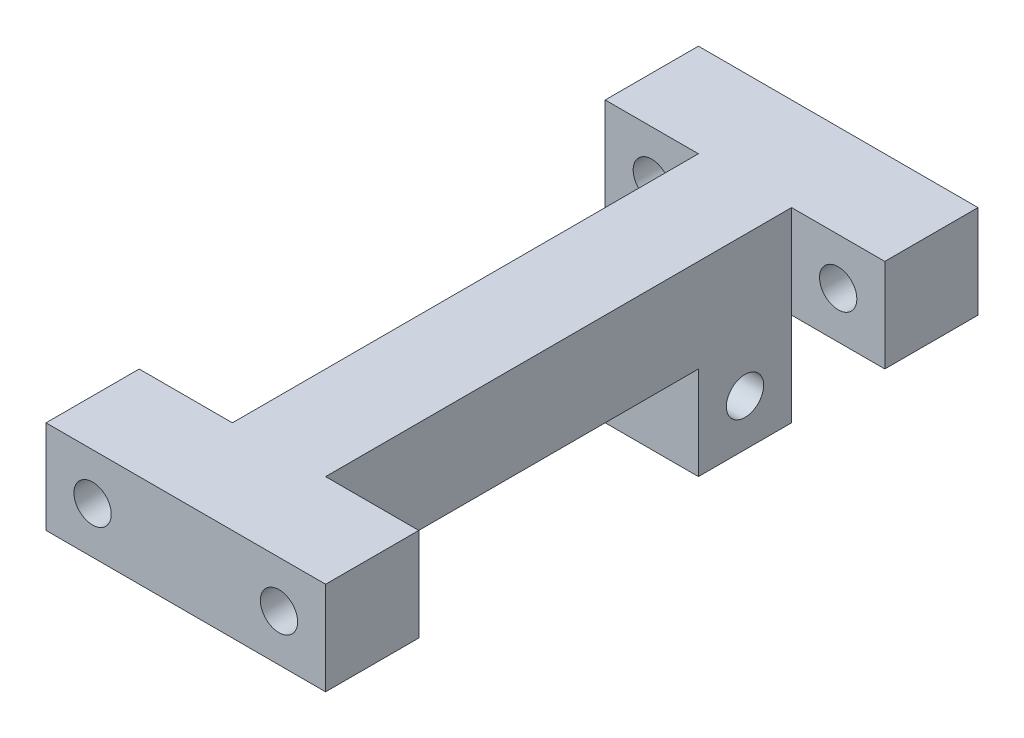
SolidWorks part; units mm, degrees
material "Cast Stainless Steel"
ref_plane "Front Plane" through (0, 0, 0) normal (0, 0, 1) x (1, 0, 0)
ref_plane "Top Plane" through (0, 0, 0) normal (0, 1, 0) x (1, 0, 0)
ref_plane "Right Plane" through (0, 0, 0) normal (1, 0, 0) x (0, 0, -1)
sketch "Sketch2" plane through (0, 0, 0) normal (1, 0, 0) x (0, 0, -1)
  line L1 (0, 0) -> (250, 0)
  line L2 (0, 0) -> (0, 100)
  line L3 (0, 100) -> (250, 100)
  line L4 (250, 0) -> (250, 100)
  dimension "D1" = 100
  dimension "D2" = 250
extrude "Boss-Extrude1" add sketch "Sketch2" along normal blind 50
sketch "Sketch3" plane through (50, 0, 0) normal (1, 0, 0) x (0, 0, -1)
  line L0 (0, 0) -> (50, 0)
  line L1 (0, 0) -> (250, 0) construction
  line L2 (250, 0) -> (200, 0)
  line L3 (50, 0) -> (50, 50)
  line L4 (50, 50) -> (200, 50)
  line L5 (200, 50) -> (200, 0)
  line L6 (50, 0) -> (200, 0)
  line M5 (0, 0) -> (250, 0)
  dimension "D1" = 50
  dimension "D2" = 50
  dimension "D3" = 50
extrude "Cut-Extrude1" cut sketch "Sketch3" against normal blind 109 contours L5 L4 L3 M5
sketch "Sketch4" plane through (50, 0, 0) normal (1, 0, 0) x (0, 0, -1)
  circle A0 centre (25, 25) radius 10
  circle A1 centre (225, 25) radius 10
  dimension "D1" = 20
  dimension "D2" = 20
extrude "Cut-Extrude2" cut sketch "Sketch4" against normal blind 109
sketch "Sketch5" plane through (50, 0, 0) normal (1, 0, 0) x (0, 0, -1)
  line L0 (250, 0) -> (250, 100) construction
  line L1 (0, 100) -> (250, 100)
  line L2 (0, 100) -> (0, 50)
  line L3 (0, 50) -> (250, 50)
  line L4 (250, 100) -> (250, 50)
extrude "Boss-Extrude2" add sketch "Sketch5" along normal blind 50
ref_plane "Plane1" through (25, 0, 0) normal (1, 0, 0) x (0, 0, -1)
mirror "Mirror1" about plane through (25, 0, 0) normal (1, 0, 0) of "Boss-Extrude2"
sketch "Sketch8" plane through (0, 0, 0) normal (0, 0, 1) x (1, 0, 0)
  line L1 (-50, 50) -> (100, 50)
  line L2 (-50, 50) -> (-50, 100)
  line L3 (-50, 100) -> (100, 100)
  line L4 (100, 50) -> (100, 100)
extrude "Boss-Extrude3" add sketch "Sketch8" along normal blind 50
sketch "Sketch9" plane through (0, 0, -250) normal (0, 0, -1) x (-1, 0, 0)
  line L1 (-100, 50) -> (50, 50)
  line L2 (-100, 50) -> (-100, 100)
  line L3 (-100, 100) -> (50, 100)
  line L4 (50, 50) -> (50, 100)
extrude "Boss-Extrude4" add sketch "Sketch9" along normal blind 50
sketch "Sketch10" plane through (0, 50, 0) normal (0, -1, 0) x (1, 0, 0)
  line L0 (100, 50) -> (100, -300) construction
  line L1 (50, 0) -> (100, 0)
  line L2 (50, 0) -> (50, -250)
  line L3 (50, -250) -> (100, -250)
  line L4 (100, 0) -> (100, -250)
  line L5 (-50, 50) -> (-50, -300) construction
  line L6 (0, 0) -> (-50, 0)
  line L7 (0, 0) -> (0, -250)
  line L8 (0, -250) -> (-50, -250)
  line L9 (-50, 0) -> (-50, -250)
  dimension "D1" = 250
extrude "Cut-Extrude5" cut sketch "Sketch10" against normal blind 50
sketch "Sketch11" plane through (0, 0, 50) normal (0, 0, 1) x (1, 0, 0)
  line L0 (-50, 100) -> (-50, 50) construction
  line L1 (100, 50) -> (100, 100) construction
  circle A0 centre (-25, 75) radius 10
  circle A1 centre (75, 75) radius 10
  dimension "D3" = 20
  dimension "D4" = 20
  dimension "D1" = 25
  dimension "D2" = 25
extrude "Cut-Extrude6" cut sketch "Sketch11" against normal blind 398
